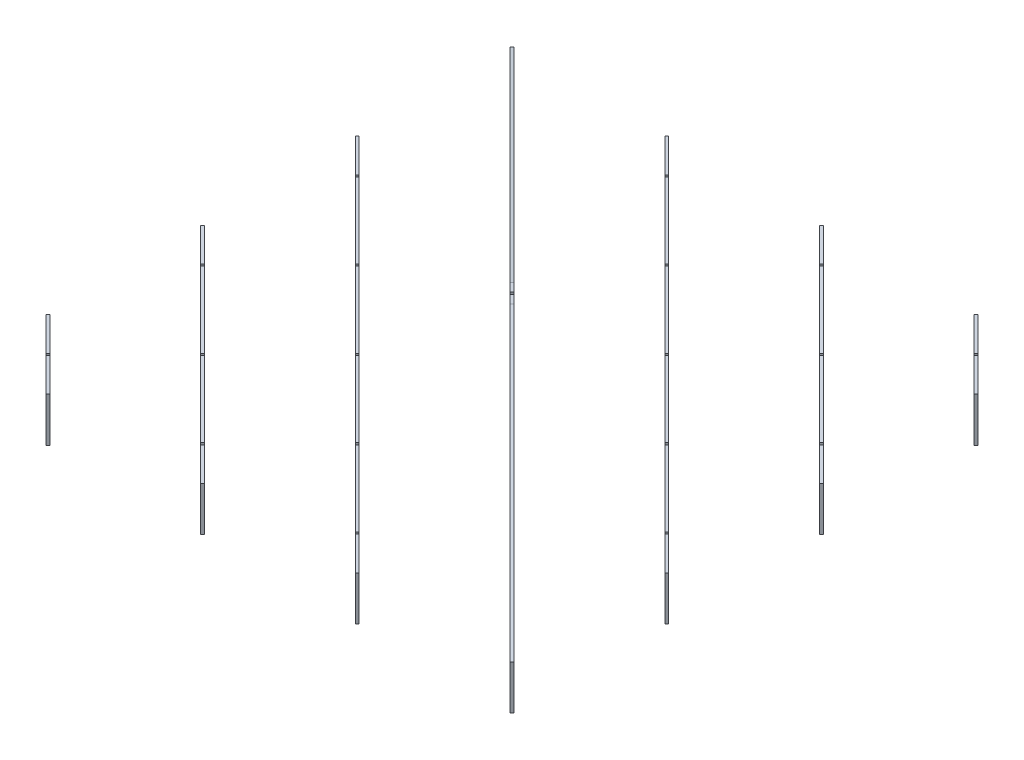
SolidWorks part; units mm, degrees
material "Plain Carbon Steel"
ref_plane "Front" through (0, 0, 0) normal (0, 0, 1) x (1, 0, 0)
ref_plane "Top" through (0, 0, 0) normal (0, 1, 0) x (1, 0, 0)
ref_plane "Right" through (0, 0, 0) normal (1, 0, 0) x (0, 0, -1)
sketch "Sketch1" plane through (0, 0, 0) normal (0, 1, 0) x (1, 0, 0)
  line L0 (-525, -525) -> (-525, 525) construction
  line L1 (-605, 605) -> (605, 605) construction
  line L2 (-605, 605) -> (-605, -605) construction
  line L3 (-605, -605) -> (605, -605) construction
  line L4 (605, 605) -> (605, -605) construction
  line L5 (-605, 605) -> (605, -605) construction
  line L6 (-605, -605) -> (605, 605) construction
  line L7 (-525, 525) -> (525, 525) construction
  line L8 (-525, 350) -> (525, 350) construction
  line L9 (-525, 175) -> (525, 175) construction
  line L10 (-525, 0) -> (525, 0) construction
  line L11 (-525, -175) -> (525, -175) construction
  line L12 (-525, -350) -> (525, -350) construction
  line L13 (-525, -525) -> (525, -525) construction
  line L14 (-350, -525) -> (-350, 525) construction
  line L15 (-175, -525) -> (-175, 525) construction
  line L16 (0, -525) -> (0, 525) construction
  line L17 (175, -525) -> (175, 525) construction
  line L18 (350, -525) -> (350, 525) construction
  line L19 (525, -525) -> (525, 525) construction
  point P0 (0, 0)
  dimension "D1" = 1210
  dimension "D2" = 1210
  dimension "D5" = 175
  dimension "D3" = 7
  dimension "D4" = 7
sketch "Sketch2" plane through (0, 0, 0) normal (0, 1, 0) x (1, 0, 0)
  line L0 (-605, 605) -> (605, -605) construction
  line L1 (602.8787, -602.8787) -> (-602.8787, -602.8787) construction
  line L2 (602.8787, -602.8787) -> (602.8787, 602.8787) construction
  line L3 (602.8787, 602.8787) -> (-602.8787, 602.8787) construction
  line L4 (-602.8787, -602.8787) -> (-602.8787, 602.8787) construction
  line L5 (602.8787, -602.8787) -> (-602.8787, 602.8787) construction
  line L6 (602.8787, 602.8787) -> (-602.8787, -602.8787) construction
  line L7 (-252.8787, 602.8787) -> (602.8787, -252.8787) construction
  line L8 (97.1213, 602.8787) -> (602.8787, 97.1213) construction
  line L9 (447.1213, 602.8787) -> (602.8787, 447.1213) construction
  line L10 (-602.8787, 252.8787) -> (252.8787, -602.8787) construction
  line L11 (-602.8787, -97.1213) -> (-97.1213, -602.8787) construction
  line L12 (-602.8787, -447.1213) -> (-447.1213, -602.8787) construction
  line L13 (-605, -449.2426) -> (-449.2426, -605)
  line L14 (-605, -99.2426) -> (-99.2426, -605)
  line L15 (-605, 250.7574) -> (250.7574, -605)
  line L16 (605, -600.7574) -> (-600.7574, 605)
  line L17 (-255, 600.7574) -> (600.7574, -255)
  line L18 (95, 600.7574) -> (600.7574, 95)
  line L19 (445, 600.7574) -> (600.7574, 445)
  line L20 (-600.7574, -445) -> (-445, -600.7574)
  line L21 (-600.7574, -95) -> (-95, -600.7574)
  line L22 (-600.7574, 255) -> (255, -600.7574)
  line L23 (600.7574, -605) -> (-605, 600.7574)
  line L24 (-250.7574, 605) -> (605, -250.7574)
  line L25 (99.2426, 605) -> (605, 99.2426)
  line L26 (449.2426, 605) -> (605, 449.2426)
  line L27 (-605, 605) -> (605, 605) construction
  line L29 (-605, -449.2426) -> (-600.7574, -445)
  line L30 (-449.2426, -605) -> (-445, -600.7574)
  line L31 (-605, -99.2426) -> (-600.7574, -95)
  line L32 (-99.2426, -605) -> (-95, -600.7574)
  line L33 (-605, 250.7574) -> (-600.7574, 255)
  line L34 (250.7574, -605) -> (255, -600.7574)
  line L35 (605, -600.7574) -> (600.7574, -605)
  line L36 (-600.7574, 605) -> (-605, 600.7574)
  line L37 (-255, 600.7574) -> (-250.7574, 605)
  line L38 (600.7574, -255) -> (605, -250.7574)
  line L39 (95, 600.7574) -> (99.2426, 605)
  line L40 (600.7574, 95) -> (605, 99.2426)
  line L41 (445, 600.7574) -> (449.2426, 605)
  line L42 (600.7574, 445) -> (605, 449.2426)
  point P0 (0, 0)
extrude "Boss-Extrude1" add sketch "Sketch2" along normal blind 100
sketch "Sketch4" plane through (-2.1213, 0, 2.1213) normal (-0.7071, 0, 0.7071) x (0.7071, 0, 0.7071)
  line L0 (0, 100) -> (0, 220) construction
  line L1 (-110.1371, 100) -> (110.1371, 100) construction
  line L2 (-30, 220) -> (-852.5992, 100)
  line L3 (-852.5992, 100) -> (-30, 100)
  line L4 (-30, 100) -> (-30, 220) construction
  line L5 (30, 220) -> (-30, 220)
  line L6 (852.5992, 100) -> (30, 100)
  line L7 (30, 220) -> (852.5992, 100)
  line L8 (-30, 100) -> (30, 100)
  dimension "D1" = 120
  dimension "D2" = 30
extrude "Boss-Extrude2" add sketch "Sketch4" against normal up to vertex
sketch "Sketch5" plane through (-527.1213, 0, 527.1213) normal (-0.7071, 0, 0.7071) x (0.7071, 0, 0.7071)
  line L0 (0, 0) -> (0, 100) construction
  line L1 (-110.1371, 100) -> (110.1371, 100) construction
  line L2 (-247.4874, 0) -> (-247.4874, 100) construction
  line L3 (494.9747, 0) -> (-247.4874, 0) construction
  line L4 (-742.4621, 0) -> (0, 0) construction
  line L5 (-357.6245, 100) -> (357.6245, 100) construction
  line L6 (-494.9747, 0) -> (-494.9747, 100) construction
  line L7 (247.4874, 0) -> (-494.9747, 0) construction
  line L8 (123.7437, 0) -> (-618.7184, 0) construction
  line L9 (-605.1118, 100) -> (605.1118, 100) construction
  line L10 (497.9747, 50) -> (491.9747, 150) construction
  line L11 (-250.4874, 150) -> (-244.4874, 150)
  line L12 (-250.4874, 150) -> (-250.4874, 50)
  line L13 (-250.4874, 50) -> (-244.4874, 50)
  line L14 (-244.4874, 150) -> (-244.4874, 50)
  line L15 (-250.4874, 150) -> (-244.4874, 50) construction
  line L16 (-250.4874, 50) -> (-244.4874, 150) construction
  line L17 (-497.9747, 150) -> (-491.9747, 150)
  line L18 (-497.9747, 150) -> (-497.9747, 50)
  line L19 (-497.9747, 50) -> (-491.9747, 50)
  line L20 (-491.9747, 150) -> (-491.9747, 50)
  line L21 (-497.9747, 150) -> (-491.9747, 50) construction
  line L22 (-497.9747, 50) -> (-491.9747, 150) construction
  line L23 (-3, 150) -> (3, 150)
  line L24 (-3, 150) -> (-3, 50)
  line L25 (-3, 50) -> (3, 50)
  line L26 (3, 150) -> (3, 50)
  line L27 (-3, 150) -> (3, 50) construction
  line L28 (-3, 50) -> (3, 150) construction
  line L29 (497.9747, 150) -> (491.9747, 50) construction
  line L30 (250.4874, 50) -> (244.4874, 150) construction
  line L31 (250.4874, 150) -> (244.4874, 50) construction
  line L32 (494.9747, 0) -> (494.9747, 100) construction
  line L33 (247.4874, 0) -> (247.4874, 100) construction
  line L34 (491.9747, 150) -> (491.9747, 50)
  line L35 (497.9747, 50) -> (491.9747, 50)
  line L36 (497.9747, 150) -> (497.9747, 50)
  line L37 (497.9747, 150) -> (491.9747, 150)
  line L38 (244.4874, 150) -> (244.4874, 50)
  line L39 (250.4874, 50) -> (244.4874, 50)
  line L40 (250.4874, 150) -> (250.4874, 50)
  line L41 (250.4874, 150) -> (244.4874, 150)
  circle A0 centre (-497.9747, 50) radius 1.5
  circle A1 centre (-491.9747, 50) radius 1.5
  circle A2 centre (-250.4874, 50) radius 1.5
  circle A3 centre (-244.4874, 50) radius 1.5
  circle A4 centre (-3, 50) radius 1.5
  circle A5 centre (3, 50) radius 1.5
  circle A6 centre (244.4874, 50) radius 1.5
  circle A7 centre (250.4874, 50) radius 1.5
  circle A8 centre (491.9747, 50) radius 1.5
  circle A9 centre (497.9747, 50) radius 1.5
  line M11 (110.1371, 100) -> (-110.1371, 100)
  dimension "D7" = 3
  dimension "D8" = 3
  dimension "D9" = 3
  dimension "D10" = 3
  dimension "D11" = 3
  dimension "D12" = 3
  dimension "D1" = 3
  dimension "D2" = 3
  dimension "D3" = 3
  dimension "D4" = 100
  dimension "D5" = 100
  dimension "D6" = 100
extrude "Cut-Extrude1" cut sketch "Sketch5" against normal up to surface (500.9747 mm away) contours L35 A9 L36 L37 L34 A8 | A8 L34 L35 | A8 L35 L34 | A9 L36 L35 | A9 L35 L36 | L39 A7 L40 L41 L38 A6 | A6 L38 L39 | A6 L39 L38 | A7 L39 L40 | A7 L40 L39 | A5 L26 L24 A4 L25 M11 | L25 A4 L24 | L24 A4 L25 | L26 A5 L25 | L25 A5 L26 | A3 L14 L11 L12 A2 L13 | L13 A2 L12 | L12 A2 L13 | L14 A3 L13 | L13 A3 L14 | A1 L20 L17 L18 A0 L19 | L19 A0 L18 | L18 A0 L19 | L20 A1 L19 | L19 A1 L20 up to face at (-172.8787, 50, 172.8787)
sketch "Sketch6" plane through (527.1213, 0, -527.1213) normal (0.7071, 0, -0.7071) x (-0.7071, 0, -0.7071)
  line L4 (-110.1371, 0) -> (110.1371, 0)
  line L5 (110.1371, 0) -> (110.1371, 100)
  line L6 (110.1371, 100) -> (-110.1371, 100)
  line L7 (-110.1371, 100) -> (-110.1371, 0)
  line L8 (-110.1371, 0) -> (110.1371, 0)
  line L9 (110.1371, 0) -> (110.1371, 100)
  line L10 (110.1371, 100) -> (-110.1371, 100)
  line L11 (-110.1371, 100) -> (-110.1371, 0)
  line L12 (497.9747, 150) -> (491.9747, 150)
  line L13 (491.9747, 150) -> (491.9747, 50)
  line L14 (491.9747, 50) -> (497.9747, 50)
  line L15 (497.9747, 50) -> (497.9747, 150)
  line L16 (497.9747, 150) -> (491.9747, 150)
  line L17 (491.9747, 150) -> (491.9747, 50)
  line L18 (491.9747, 50) -> (497.9747, 50)
  line L19 (497.9747, 50) -> (497.9747, 150)
  line L20 (250.4874, 150) -> (244.4874, 150)
  line L21 (244.4874, 150) -> (244.4874, 50)
  line L22 (244.4874, 50) -> (250.4874, 50)
  line L23 (250.4874, 50) -> (250.4874, 150)
  line L24 (250.4874, 150) -> (244.4874, 150)
  line L25 (244.4874, 150) -> (244.4874, 50)
  line L26 (244.4874, 50) -> (250.4874, 50)
  line L27 (250.4874, 50) -> (250.4874, 150)
  line L28 (-244.4874, 50) -> (-244.4874, 150)
  line L29 (-250.4874, 50) -> (-244.4874, 50)
  line L30 (-250.4874, 150) -> (-250.4874, 50)
  line L31 (-244.4874, 150) -> (-250.4874, 150)
  line L32 (-244.4874, 50) -> (-244.4874, 150)
  line L33 (-250.4874, 50) -> (-244.4874, 50)
  line L34 (-250.4874, 150) -> (-250.4874, 50)
  line L35 (-244.4874, 150) -> (-250.4874, 150)
  line L36 (-491.9747, 50) -> (-491.9747, 150)
  line L37 (-497.9747, 50) -> (-491.9747, 50)
  line L38 (-497.9747, 150) -> (-497.9747, 50)
  line L39 (-491.9747, 150) -> (-497.9747, 150)
  line L40 (-491.9747, 50) -> (-491.9747, 150)
  line L41 (-497.9747, 50) -> (-491.9747, 50)
  line L42 (-497.9747, 150) -> (-497.9747, 50)
  line L43 (-491.9747, 150) -> (-497.9747, 150)
  line L44 (3, 150) -> (-3, 150)
  line L45 (3, 50) -> (3, 150)
  line L46 (-3, 50) -> (3, 50)
  line L47 (-3, 150) -> (-3, 50)
  line L48 (3, 150) -> (-3, 150)
  line L49 (3, 50) -> (3, 150)
  line L50 (-3, 50) -> (3, 50)
  line L51 (-3, 150) -> (-3, 50)
  circle A1 centre (-3, 50) radius 1.5
  circle A2 centre (-3, 50) radius 1.5
  circle A3 centre (3, 50) radius 1.5
  circle A4 centre (3, 50) radius 1.5
  circle A5 centre (244.4874, 50) radius 1.5
  circle A6 centre (244.4874, 50) radius 1.5
  circle A7 centre (250.4874, 50) radius 1.5
  circle A8 centre (250.4874, 50) radius 1.5
  circle A9 centre (491.9747, 50) radius 1.5
  circle A10 centre (491.9747, 50) radius 1.5
  circle A11 centre (497.9747, 50) radius 1.5
  circle A12 centre (497.9747, 50) radius 1.5
  circle A13 centre (-497.9747, 50) radius 1.5
  circle A14 centre (-497.9747, 50) radius 1.5
  circle A15 centre (-491.9747, 50) radius 1.5
  circle A16 centre (-491.9747, 50) radius 1.5
  circle A17 centre (-250.4874, 50) radius 1.5
  circle A18 centre (-250.4874, 50) radius 1.5
  circle A19 centre (-244.4874, 50) radius 1.5
  circle A20 centre (-244.4874, 50) radius 1.5
  dimension "D1" = 0
  dimension "D2" = 0
  dimension "D3" = 0
  dimension "D4" = 0
  dimension "D5" = 0
  dimension "D6" = 0
  dimension "D7" = 0
  dimension "D8" = 0
  dimension "D9" = 0
  dimension "D10" = 0
  dimension "D11" = 0
  dimension "D12" = 0
  dimension "D13" = 0
  dimension "D14" = 0
  dimension "D15" = 0
  dimension "D16" = 0
extrude "Cut-Extrude2" cut sketch "Sketch6" against normal up to surface (500.9747 mm away) contours A16 L40 L43 L42 A14 L41 | L41 A14 L42 | L42 A14 L41 | L40 A16 L41 | L41 A16 L40 | A20 L32 L35 L34 A18 L33 | L33 A18 L34 | L34 A18 L33 | L32 A20 L33 | L33 A20 L32 | A4 L49 L10 L51 A2 L50 | L49 A4 L50 | L50 A4 L49 | L50 A2 L51 | L51 A2 L50 | L25 A6 L26 | L26 A6 L25 | A8 L27 L24 L25 A6 L26 | L27 A8 L26 | L26 A8 L27 | L17 A10 L18 | L18 A10 L17 | A12 L19 L16 L17 A10 L18 | L19 A12 L18 | L18 A12 L19 up to face at (172.8787, 50, -172.8787)
sketch "Sketch7" plane through (-2.1213, 0, 2.1213) normal (-0.7071, 0, 0.7071) x (0.7071, 0, 0.7071)
  line L0 (0, 220) -> (0, 0) construction
  line L1 (30, 220) -> (-30, 220) construction
  line L2 (123.7437, 0) -> (-618.7184, 0) construction
  line L3 (-3, 330) -> (3, 330)
  line L4 (-3, 330) -> (-3, 110)
  line L5 (-3, 110) -> (3, 110)
  line L6 (3, 330) -> (3, 110)
  line L7 (-3, 330) -> (3, 110) construction
  line L8 (-3, 110) -> (3, 330) construction
  line L9 (-250.4874, 50) -> (-244.4874, 50)
  line L10 (-250.4874, 50) -> (-250.4874, -50)
  line L11 (-250.4874, -50) -> (-244.4874, -50)
  line L12 (-244.4874, 50) -> (-244.4874, -50)
  line L13 (-250.4874, 50) -> (-244.4874, -50) construction
  line L14 (-250.4874, -50) -> (-244.4874, 50) construction
  line L15 (247.4874, 0) -> (-494.9747, 0) construction
  line L16 (-497.9747, 50) -> (-491.9747, 50)
  line L17 (-497.9747, 50) -> (-497.9747, -50)
  line L18 (-497.9747, -50) -> (-491.9747, -50)
  line L19 (-491.9747, 50) -> (-491.9747, -50)
  line L20 (-497.9747, 50) -> (-491.9747, -50) construction
  line L21 (-497.9747, -50) -> (-491.9747, 50) construction
  line L22 (-855.5992, 0) -> (855.5992, 0) construction
  line L23 (-742.4621, 0) -> (0, 0) construction
  line L24 (-745.4621, 50) -> (-739.4621, 50)
  line L25 (-745.4621, 50) -> (-745.4621, -50)
  line L26 (-745.4621, -50) -> (-739.4621, -50)
  line L27 (-739.4621, 50) -> (-739.4621, -50)
  line L28 (-745.4621, 50) -> (-739.4621, -50) construction
  line L29 (-745.4621, -50) -> (-739.4621, 50) construction
  line L30 (745.4621, -50) -> (739.4621, 50) construction
  line L31 (745.4621, 50) -> (739.4621, -50) construction
  line L32 (497.9747, -50) -> (491.9747, 50) construction
  line L33 (497.9747, 50) -> (491.9747, -50) construction
  line L34 (250.4874, -50) -> (244.4874, 50) construction
  line L35 (250.4874, 50) -> (244.4874, -50) construction
  line L36 (739.4621, 50) -> (739.4621, -50)
  line L37 (745.4621, -50) -> (739.4621, -50)
  line L38 (745.4621, 50) -> (745.4621, -50)
  line L39 (745.4621, 50) -> (739.4621, 50)
  line L40 (491.9747, 50) -> (491.9747, -50)
  line L41 (497.9747, -50) -> (491.9747, -50)
  line L42 (497.9747, 50) -> (497.9747, -50)
  line L43 (497.9747, 50) -> (491.9747, 50)
  line L44 (244.4874, 50) -> (244.4874, -50)
  line L45 (250.4874, -50) -> (244.4874, -50)
  line L46 (250.4874, 50) -> (250.4874, -50)
  line L47 (250.4874, 50) -> (244.4874, 50)
  circle A0 centre (-3, 110) radius 1.5
  circle A1 centre (3, 110) radius 1.5
  circle A2 centre (-250.4874, 50) radius 1.5
  circle A3 centre (-244.4874, 50) radius 1.5
  circle A4 centre (-491.9747, 50) radius 1.5
  circle A5 centre (-497.9747, 50) radius 1.5
  circle A6 centre (-739.4621, 50) radius 1.5
  circle A7 centre (-745.4621, 50) radius 1.5
  circle A8 centre (745.4621, 50) radius 1.5
  circle A9 centre (739.4621, 50) radius 1.5
  circle A10 centre (497.9747, 50) radius 1.5
  circle A11 centre (491.9747, 50) radius 1.5
  circle A12 centre (244.4874, 50) radius 1.5
  circle A13 centre (250.4874, 50) radius 1.5
  point P9 (-247.4874, 0)
  point P16 (-494.9747, 0)
  point P25 (-742.4621, 0)
  point P32 (0, 110)
  point P59 (742.4621, 0)
  point P60 (494.9747, 0)
  point P61 (247.4874, 0)
  line M15 (-852.5992, 0) -> (852.5992, 0)
  line M18 (30, 220) -> (-30, 220)
  dimension "D7" = 3
  dimension "D8" = 3
  dimension "D9" = 3
  dimension "D10" = 3
  dimension "D11" = 3
  dimension "D12" = 3
  dimension "D1" = 3
  dimension "D3" = 3
  dimension "D4" = 100
  dimension "D6" = 100
  dimension "D13" = 3
  dimension "D14" = 3
  dimension "D15" = 3
  dimension "D2" = 100
  dimension "D5" = 3
extrude "Cut-Extrude3" cut sketch "Sketch7" against normal up to next (6 mm away) contours L24 A7 L25 | L25 A7 L24 | A7 L25 L27 A6 L24 M15 | L24 A6 L27 | L27 A6 L24 | L16 A5 L17 | L17 A5 L16 | A5 L17 L19 A4 L16 M15 | L16 A4 L19 | L19 A4 L16 | L12 A3 L9 | L9 A3 L12 | A3 L9 A2 L10 L12 M15 | L10 A2 L9 | L9 A2 L10 | A1 L6 L4 A0 L5 M18 | L5 A0 L4 | L4 A0 L5 | L5 A1 L6 | L6 A1 L5 | A12 L44 L47 | A12 L47 L44 | L46 A13 L47 A12 L44 M15 | A13 L46 L47 | A13 L47 L46 | A11 L40 L43 | A11 L43 L40 | L43 A11 L40 L42 A10 M15 | A10 L42 L43 | A10 L43 L42 | A9 L36 L39 | A9 L39 L36 | L39 A9 L36 L38 A8 M15 | A8 L38 L39 | A8 L39 L38
sketch "Sketch8" plane through (-2.1213, 0, 2.1213) normal (-0.7071, 0, 0.7071) x (0.7071, 0, 0.7071)
  line L0 (346.2311, 22) -> (396.2311, 22) construction
  line L1 (346.2311, 19) -> (346.2311, 25) construction
  line L2 (396.2311, 25) -> (396.2311, 19) construction
  line L3 (371.2311, 25) -> (371.2311, 19) construction
  line L4 (386.2311, 25) -> (356.2311, 25) construction
  line L5 (356.2311, 19) -> (386.2311, 19) construction
  line L6 (0, 0) -> (0, 262.5502) construction
  line L7 (343.2311, 28) -> (399.2311, 28)
  line L8 (343.2311, 28) -> (343.2311, 16)
  line L9 (343.2311, 16) -> (399.2311, 16)
  line L10 (399.2311, 28) -> (399.2311, 16)
  line L11 (343.2311, 28) -> (399.2311, 16) construction
  line L12 (343.2311, 16) -> (399.2311, 28) construction
  line L13 (-343.2311, 16) -> (-399.2311, 28) construction
  line L14 (-343.2311, 28) -> (-399.2311, 16) construction
  line L15 (-371.2311, 25) -> (-371.2311, 19) construction
  line L16 (-346.2311, 22) -> (-396.2311, 22) construction
  line L17 (-399.2311, 28) -> (-399.2311, 16)
  line L18 (-343.2311, 16) -> (-399.2311, 16)
  line L19 (-343.2311, 28) -> (-343.2311, 16)
  line L20 (-343.2311, 28) -> (-399.2311, 28)
  point P12 (371.2311, 22)
  point P28 (-371.2311, 22)
  dimension "D1" = 3
  dimension "D2" = 3
extrude "Cut-Extrude4" cut sketch "Sketch8" against normal up to next (6 mm away)
sketch "Sketch9" plane through (2.1213, 0, -2.1213) normal (0.7071, 0, -0.7071) x (-0.7071, 0, -0.7071)
  line L0 (123.7437, 74) -> (-123.7437, 74) construction
  line L1 (0, 0) -> (0, 292.3791) construction
  circle A0 centre (123.7437, 64) radius 4
  circle A1 centre (123.7437, 84) radius 4
  circle A2 centre (40, 74) radius 10
  circle A3 centre (-40, 74) radius 10
  circle A4 centre (-123.7437, 84) radius 4
  circle A5 centre (-123.7437, 64) radius 4
  dimension "D1" = 8
  dimension "D2" = 20
  dimension "D3" = 80
extrude "Cut-Extrude5" cut sketch "Sketch9" against normal up to next (6 mm away)
sketch "Sketch10" plane through (177.1213, 0, -177.1213) normal (0.7071, 0, -0.7071) x (-0.7071, 0, -0.7071)
  line L0 (371.2311, 100) -> (371.2311, 0) construction
  line L1 (250.4874, 100) -> (491.9747, 100) construction
  line L2 (-605.1118, 0) -> (605.1118, 0) construction
  line L3 (123.7437, 100) -> (123.7437, 0) construction
  line L4 (3, 100) -> (244.4874, 100) construction
  line L5 (-123.7437, 100) -> (-123.7437, 0) construction
  line L6 (-244.4874, 100) -> (-3, 100) construction
  line L7 (-371.2311, 100) -> (-371.2311, 0) construction
  line L8 (-491.9747, 100) -> (-250.4874, 100) construction
  circle A0 centre (371.2311, 50) radius 3
  circle A1 centre (123.7437, 50) radius 3
  circle A2 centre (-123.7437, 50) radius 3
  circle A3 centre (-371.2311, 50) radius 3
  dimension "D1" = 6
extrude "Cut-Extrude6" cut sketch "Sketch10" along normal up to surface (253.4874 mm away) from surface
ref_plane "Plane1" through (0, 0, 0) normal (0.7071, 0, -0.7071) x (-0.7071, 0, -0.7071)
mirror "Mirror1" about plane through (0, 0, 0) normal (0.7071, 0, -0.7071) of "Cut-Extrude6"
equation "\"D1@Boss-Extrude1\"=\"Plate width\""
equation "\"Plate width\"=100"
equation "\"D1@Sketch5\"=\"Half rib thickness\""
equation "\"D2@Sketch5\"=\"Half rib thickness\""
equation "\"D3@Sketch5\"=\"Half rib thickness\""
equation "\"D4@Sketch5\"=\"Plate width\""
equation "\"D5@Sketch5\"=\"Plate width\""
equation "\"D6@Sketch5\"=\"Plate width\""
equation "\"D7@Sketch5\"=\"Half rib thickness\""
equation "\"D8@Sketch5\"=\"Half rib thickness\""
equation "\"D9@Sketch5\"=\"Half rib thickness\""
equation "\"D10@Sketch5\"=\"Half rib thickness\""
equation "\"D11@Sketch5\"=\"Half rib thickness\""
equation "\"D12@Sketch5\"=\"Half rib thickness\""
equation "\"D1@Sketch7\"=\"Half rib thickness\""
equation "\"D2@Sketch7\"=\"Plate width\""
equation "\"D3@Sketch7\"=\"Half rib thickness\""
equation "\"D4@Sketch7\"=\"Plate width\""
equation "\"D5@Sketch7\"=\"Half rib thickness\""
equation "\"D6@Sketch7\"=\"Plate width\""
equation "\"D7@Sketch7\"=\"Half rib thickness\""
equation "\"D8@Sketch7\"=\"Half rib thickness\""
equation "\"D9@Sketch7\"=\"Half rib thickness\""
equation "\"D10@Sketch7\"=\"Half rib thickness\""
equation "\"D11@Sketch7\"=\"Half rib thickness\""
equation "\"D12@Sketch7\"=\"Half rib thickness\""
equation "\"D13@Sketch7\"=\"Half rib thickness\""
equation "\"D14@Sketch7\"=\"Half rib thickness\""
equation "\"D15@Sketch7\"=\"Half rib thickness\""
